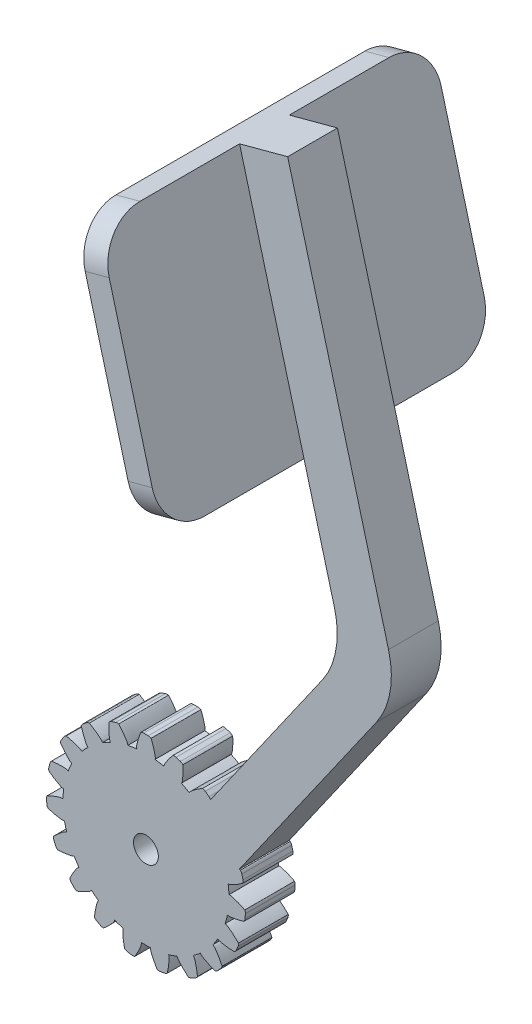
SolidWorks part; units mm, degrees
ref_plane "Front Plane" through (0, 0, 0) normal (0, 0, 1) x (1, 0, 0)
ref_plane "Top Plane" through (0, 0, 0) normal (0, 1, 0) x (1, 0, 0)
ref_plane "Right Plane" through (0, 0, 0) normal (1, 0, 0) x (0, 0, -1)
sketch "Sketch1" plane through (0, 0, 0) normal (0, 0, 1) x (1, 0, 0)
  line L1 (0.275, 11.9993) -> (-0.275, 11.9993)
  circle A0 centre (0, 0) radius 1.5
  arc A1 (-1.1, 9.9393) -> (1.1, 9.9393) centre (0, 0) ccw
  arc A2 (-0.62, 11.9) -> (-0.275, 11.9993) centre (-0.275, 11.3504) cw
  arc A3 (0.62, 11.9) -> (0.275, 11.9993) centre (0.275, 11.3504) ccw
  spline S0 degree 3 poles (-1.1, 9.9393) (-1.2753, 10.1839) (-0.6644, 11.8721) (-0.62, 11.9) knots 0 0 0 0 1 1 1 1
  spline S1 degree 3 poles (1.1, 9.9393) (1.2753, 10.1839) (0.6644, 11.8721) (0.62, 11.9) knots 0 0 0 0 1 1 1 1
  point P11 (0, 0)
  point P12 (0, 0)
  dimension "D1" = 3
  dimension "D2" = 20
  dimension "D10" = 0.6489
  dimension "D3" = 2.06
  dimension "D8" = 10.8
  dimension "D9" = 1.1
extrude "Boss-Extrude1" add sketch "Sketch1" along normal blind 6
pattern_circular "CirPattern1" count 19 over 360 about axis through (0, 0, 6) along (0, 0, -1) of "Boss-Extrude1"
sketch "Sketch2" plane through (0, 0, 0) normal (0, 0, 1) x (1, 0, 0)
  line L0 (0, 0) -> (8.758, 0) construction
  line L1 (8.758, 0) -> (3.8431, 3.4415)
  line L2 (8.758, 0) -> (27.7633, 27.1424)
  line L3 (3.8431, 3.4415) -> (21.2436, 28.292)
  line L4 (22.7113, 36.616) -> (11.2819, 79.2713)
  line L5 (29.231, 35.4664) -> (17.0774, 80.8242)
  line L6 (17.0774, 80.8242) -> (11.2819, 79.2713)
  arc A0 (27.7633, 27.1424) -> (29.231, 35.4664) centre (19.5718, 32.8782) ccw
  arc A1 (21.2436, 28.292) -> (22.7113, 36.616) centre (13.0521, 34.0278) ccw
  point P12 (23.9182, 32.1118)
  dimension "D5" = 10
  dimension "D1" = 35
  dimension "D2" = 6
  dimension "D3" = 35
  dimension "D4" = 130
  dimension "D6" = 6
  dimension "D7" = 44.16
extrude "Boss-Extrude2" add sketch "Sketch2" along normal blind 6
sketch "Sketch3" plane through (30.344, 8.1306, 0) normal (-0.9659, -0.2588, 0) x (0, 0, 1)
  line L0 (3, 73.6502) -> (3, 58.6502) construction
  line L1 (6, 73.6502) -> (0, 73.6502) construction
  line L3 (-12, 43.6502) -> (18, 43.6502)
  line L4 (-17, 48.6502) -> (-17, 68.6502)
  line L5 (-12, 73.6502) -> (18, 73.6502)
  line L6 (23, 48.6502) -> (23, 68.6502)
  line L7 (-17, 43.6502) -> (23, 73.6502) construction
  line L8 (-17, 73.6502) -> (23, 43.6502) construction
  arc A0 (-12, 43.6502) -> (-17, 48.6502) centre (-12, 48.6502) cw
  arc A1 (18, 43.6502) -> (23, 48.6502) centre (18, 48.6502) ccw
  arc A2 (18, 73.6502) -> (23, 68.6502) centre (18, 68.6502) cw
  arc A3 (-17, 68.6502) -> (-12, 73.6502) centre (-12, 68.6502) cw
  point P8 (3, 73.6502)
  dimension "D3" = 5
  dimension "D1" = 40
  dimension "D2" = 30
extrude "Boss-Extrude3" add sketch "Sketch3" along normal blind 3
